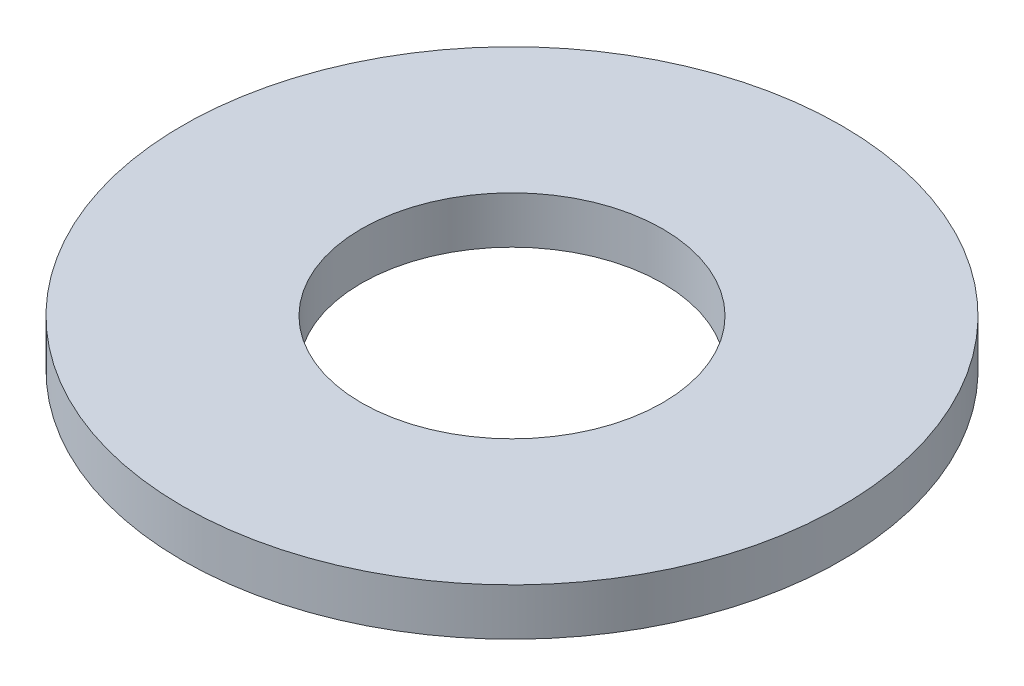
SolidWorks part; units mm, degrees
material "Stop odlewniczy stali"
ref_plane "Płaszczyzna przednia" through (0, 0, 0) normal (0, 0, 1) x (1, 0, 0)
ref_plane "Płaszczyzna górna" through (0, 0, 0) normal (0, 1, 0) x (1, 0, 0)
ref_plane "Płaszczyzna prawa" through (0, 0, 0) normal (1, 0, 0) x (0, 0, -1)
sketch "Szkic2" plane through (0, 0, 0) normal (0, 1, 0) x (1, 0, 0)
  circle A0 centre (0, 0) radius 3.5
  circle A1 centre (0, 0) radius 1.6
extrude "Dodanie-wyciągnięcie1" add sketch "Szkic2" along normal blind 0.5
